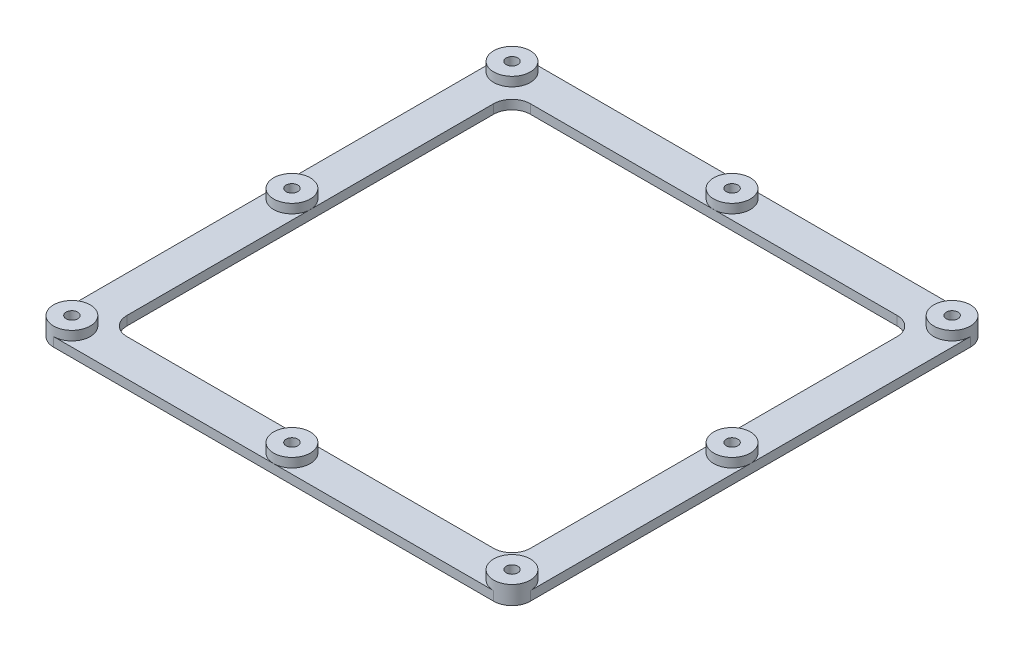
SolidWorks part; units mm, degrees
material "5052-H32"
ref_plane "Front Plane" through (0, 0, 0) normal (0, 0, 1) x (1, 0, 0)
ref_plane "Top Plane" through (0, 0, 0) normal (0, 1, 0) x (1, 0, 0)
ref_plane "Right Plane" through (0, 0, 0) normal (1, 0, 0) x (0, 0, -1)
sketch "Sketch1" plane through (0, 0, 0) normal (0, 1, 0) x (1, 0, 0)
  line L1 (82.55, -82.55) -> (-82.55, -82.55)
  line L2 (82.55, -82.55) -> (82.55, 82.55)
  line L3 (82.55, 82.55) -> (-82.55, 82.55)
  line L4 (-82.55, -82.55) -> (-82.55, 82.55)
  line L5 (82.55, -82.55) -> (-82.55, 82.55) construction
  line L6 (82.55, 82.55) -> (-82.55, -82.55) construction
  line L7 (69.85, -69.85) -> (-69.85, -69.85)
  line L8 (69.85, -69.85) -> (69.85, 69.85)
  line L9 (69.85, 69.85) -> (-69.85, 69.85)
  line L10 (-69.85, -69.85) -> (-69.85, 69.85)
  line L11 (69.85, -69.85) -> (-69.85, 69.85) construction
  line L12 (69.85, 69.85) -> (-69.85, -69.85) construction
  point P0 (0, 0)
  point P6 (0, 0)
  dimension "D1" = 139.7
  dimension "D2" = 139.7
  dimension "D3" = 12.7
  dimension "D4" = 12.7
extrude "Boss-Extrude1" add sketch "Sketch1" along normal blind 6.35
fillet "Fillet1" radius 6.35 8 edges at (-69.85, 3.175, 69.85) (-69.85, 3.175, -69.85) (69.85, 3.175, -69.85) (69.85, 3.175, 69.85) (82.55, 3.175, 82.55) (82.55, 3.175, -82.55) (-82.55, 3.175, -82.55) (-82.55, 3.175, 82.55)
hole_wizard "#10-32 Tapped Hole1" positions "Sketch2" profile "Sketch3" tap size "#10-32" standard "ANSI Inch" end condition through all
sketch "Sketch2" plane through (0, 6.35, 0) normal (0, 1, 0) x (1, 0, 0)
  line L0 (-76.2, -76.2) -> (-76.2, 76.2)
  line L1 (-76.2, 76.2) -> (76.2, 76.2)
  line L2 (76.2, 76.2) -> (76.2, -76.2)
  line L3 (76.2, -76.2) -> (-76.2, -76.2)
  point P0 (-76.2, -76.2)
  point P3 (-76.2, 76.2)
  point P6 (76.2, 76.2)
  point P9 (76.2, -76.2)
  point P19 (-76.2, 0)
  point P21 (0, 76.2)
  point P23 (76.2, 0)
  point P25 (0, -76.2)
sketch "Sketch3" plane through (-76.2, 6.35, 76.2) normal (1, 0, 0) x (0, 0, 1)
  line L0 (0, 0) -> (0, 6.35)
  line L1 (0, 6.35) -> (2.0193, 6.35)
  line L2 (2.0193, 6.35) -> (2.0193, 0)
  line L5 (2.0193, 0) -> (0, 0)
  line L11 (0, -6.35) -> (0, 107.95) construction
  dimension "Thread Major Dia." = 4.0386
  dimension "Thru Tap Drill Depth" = 6.35
sketch "Sketch4" plane through (0, 6.35, 0) normal (0, 1, 0) x (1, 0, 0)
  circle A0 centre (-76.2, 76.2) radius 6.35
  circle A1 centre (-76.2, 0) radius 6.35
  circle A2 centre (-76.2, -76.2) radius 6.35
  circle A3 centre (0, -76.2) radius 6.35
  circle A4 centre (76.2, -76.2) radius 6.35
  circle A5 centre (76.2, 0) radius 6.35
  circle A6 centre (76.2, 76.2) radius 6.35
  circle A7 centre (0, 76.2) radius 6.35
extrude "Cut-Extrude1" cut sketch "Sketch4" against normal blind 3.175 flip side to cut
